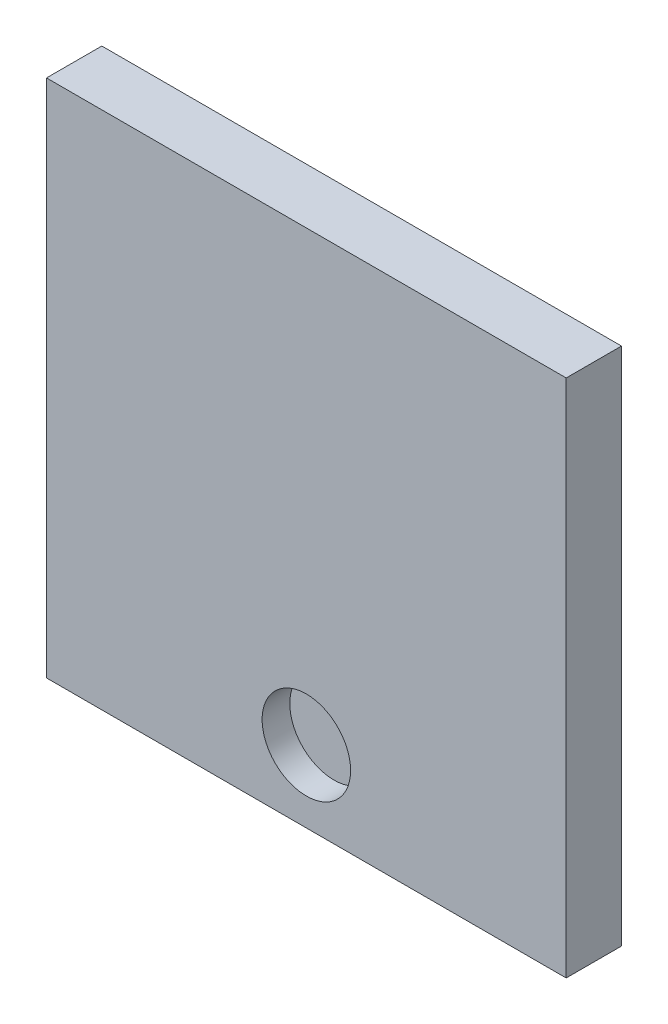
SolidWorks part; units mm, degrees
ref_plane "Piano frontale" through (0, 0, 0) normal (0, 0, 1) x (1, 0, 0)
ref_plane "Piano superiore" through (0, 0, 0) normal (0, 1, 0) x (1, 0, 0)
ref_plane "Piano destro" through (0, 0, 0) normal (1, 0, 0) x (0, 0, -1)
sketch "Schizzo1" plane through (0, 0, 0) normal (0, 0, 1) x (1, 0, 0)
  line L1 (47, -47) -> (-47, -47)
  line L2 (47, -47) -> (47, 47)
  line L3 (47, 47) -> (-47, 47)
  line L4 (-47, -47) -> (-47, 47)
  line L5 (47, -47) -> (-47, 47) construction
  line L6 (47, 47) -> (-47, -47) construction
  point P0 (0, 0)
  dimension "D1" = 94
  dimension "D2" = 94
extrude "Estrusione-Estrusione1" add sketch "Schizzo1" along normal blind 10
sketch "Schizzo2" plane through (0, 0, 10) normal (0, 0, 1) x (1, 0, 0)
  line L1 (34.8662, 26.2414) -> (-34.8662, 26.2414)
  line L2 (34.8662, 26.2414) -> (34.8662, -26.2414)
  line L3 (34.8662, -26.2414) -> (-34.8662, -26.2414)
  line L4 (-34.8662, 26.2414) -> (-34.8662, -26.2414)
  line L5 (34.8662, 26.2414) -> (-34.8662, -26.2414) construction
  line L6 (34.8662, -26.2414) -> (-34.8662, 26.2414) construction
  point P0 (0, 0)
sketch "Schizzo3" plane through (0, 0, 10) normal (0, 0, 1) x (1, 0, 0)
  circle A0 centre (0, -34) radius 8
extrude "Taglio-Estrusione1" cut sketch "Schizzo3" against normal blind 5
